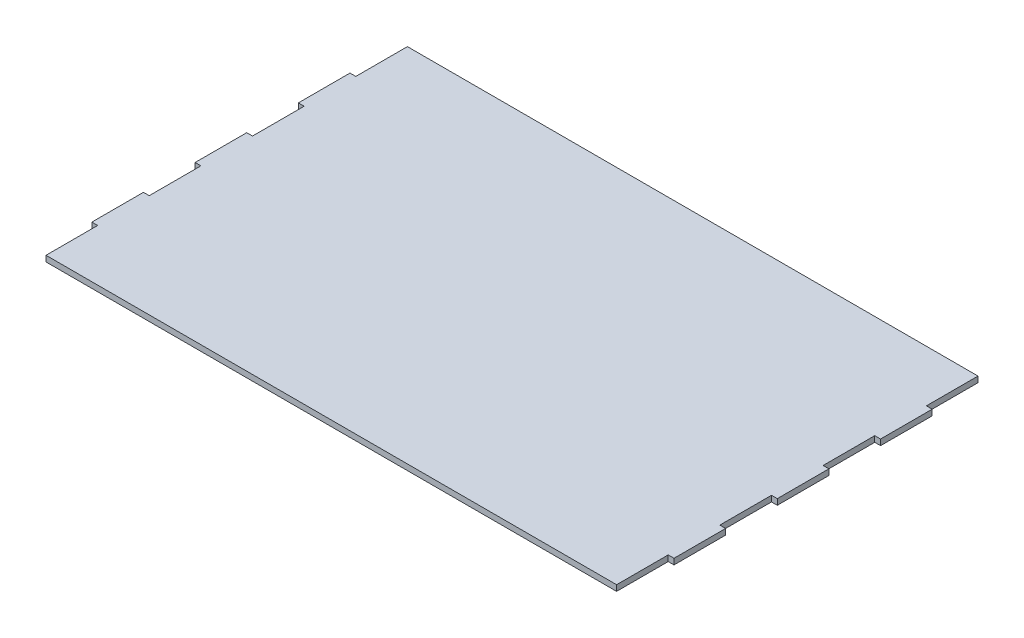
SolidWorks part; units mm, degrees
ref_plane "Alzado" through (0, 0, 0) normal (0, 0, 1) x (1, 0, 0)
ref_plane "Planta" through (0, 0, 0) normal (0, 1, 0) x (1, 0, 0)
ref_plane "Vista lateral" through (0, 0, 0) normal (1, 0, 0) x (0, 0, -1)
sketch "Croquis2" plane through (0, 0, 0) normal (0, 1, 0) x (1, 0, 0)
  line L2 (-136.1862, -58.8098) -> (158.8881, -58.8098)
  line L4 (-136.1862, -32.1098) -> (-136.1862, -58.8098)
  line L5 (11.351, -58.8098) -> (11.351, 39.9531) construction
  line L6 (-136.1862, -5.4098) -> (-139.1862, -5.4098)
  line L7 (-139.1862, -5.4098) -> (-139.1862, -32.1098)
  line L8 (-136.1862, -32.1098) -> (-139.1862, -32.1098)
  line L38 (-136.1862, -5.4098) -> (-136.1862, 21.2902)
  line L39 (-136.1862, 21.2902) -> (-139.1862, 21.2902)
  line L40 (-139.1862, 21.2902) -> (-139.1862, 47.9902)
  line L41 (-139.1862, 47.9902) -> (-136.1862, 47.9902)
  line L42 (-136.1862, 47.9902) -> (-136.1862, 74.6902)
  line L43 (-136.1862, 74.6902) -> (-139.1862, 74.6902)
  line L44 (-139.1862, 74.6902) -> (-139.1862, 101.3902)
  line L45 (-139.1862, 101.3902) -> (-136.1862, 101.3902)
  line L46 (-136.1862, 101.3902) -> (-136.1862, 128.0902)
  line L47 (158.8881, 101.3902) -> (158.8881, 128.0902)
  line L48 (161.8881, 101.3902) -> (158.8881, 101.3902)
  line L49 (161.8881, 74.6902) -> (161.8881, 101.3902)
  line L50 (158.8881, 74.6902) -> (161.8881, 74.6902)
  line L51 (158.8881, 47.9902) -> (158.8881, 74.6902)
  line L52 (161.8881, 47.9902) -> (158.8881, 47.9902)
  line L53 (161.8881, 21.2902) -> (161.8881, 47.9902)
  line L54 (158.8881, 21.2902) -> (161.8881, 21.2902)
  line L55 (158.8881, -5.4098) -> (158.8881, 21.2902)
  line L56 (158.8881, -32.1098) -> (161.8881, -32.1098)
  line L57 (161.8881, -5.4098) -> (161.8881, -32.1098)
  line L58 (158.8881, -5.4098) -> (161.8881, -5.4098)
  line L59 (158.8881, -32.1098) -> (158.8881, -58.8098)
  line L60 (-136.1862, 128.0902) -> (158.8881, 128.0902)
  point P3 (0, 21.2902)
  point P18 (11.351, 11.3948)
extrude "Saliente-Extruir1" add sketch "Croquis2" along normal blind 3
